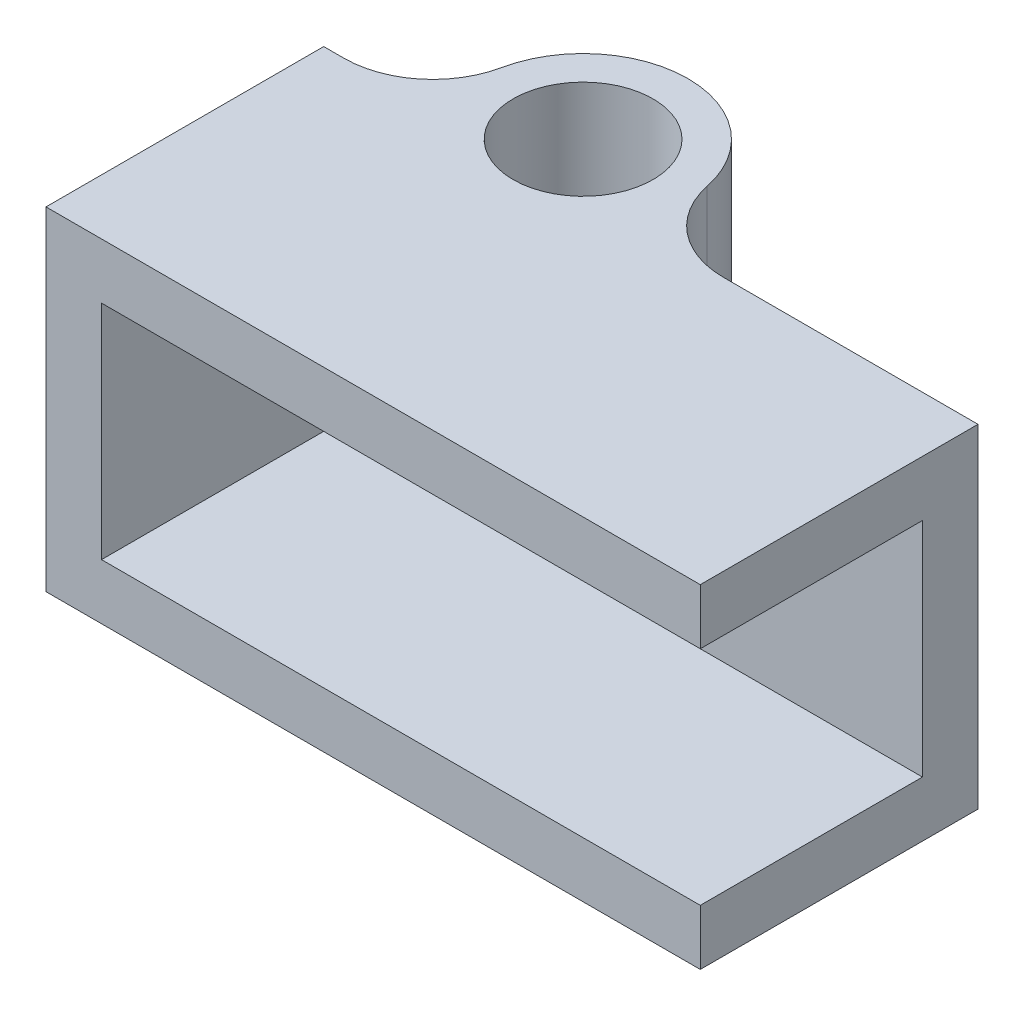
SolidWorks part; units mm, degrees
material "LWPLA"
ref_plane "Front Plane" through (0, 0, 0) normal (0, 0, 1) x (1, 0, 0)
ref_plane "Top Plane" through (0, 0, 0) normal (0, 1, 0) x (1, 0, 0)
ref_plane "Right Plane" through (0, 0, 0) normal (1, 0, 0) x (0, 0, -1)
sketch "Sketch1" plane through (0, 0, 0) normal (0, 1, 0) x (1, 0, 0)
  line L0 (-12.7, -3) -> (12.7, -3)
  line L1 (-12.7, -3) -> (-12.7, -1.4125)
  line L2 (-12.7, -1.4125) -> (-2.6467, -1.4125)
  line L3 (0, -3) -> (0, 3) construction
  line L4 (12.7, -3) -> (12.7, -1.4125)
  line L5 (12.7, -1.4125) -> (2.6467, -1.4125)
  line L6 (0, -3) -> (-6, -3)
  line L7 (-6, -3) -> (-6, -1.4125)
  circle A0 centre (0, 0) radius 2
  circle A1 centre (0, 0) radius 3
  point P7 (0, -3)
  dimension "D1" = 4
  dimension "D2" = 6
  dimension "D3" = 25.4
  dimension "D4" = 1.5875
  dimension "D5" = 6
extrude "Boss-Extrude1" add sketch "Sketch1" along normal blind 9.525 contours A1 L2 L7 L0 | A1 L0 L4 L5 | L3 A1 A0 | A1 L3 A0
fillet "Fillet1" radius 2.54 2 edges at (-2.6467, 4.7625, 1.4125) (2.6467, 4.7625, 1.4125)
sketch "Sketch2" plane through (0, 0, 3) normal (0, 0, 1) x (1, 0, 0)
  line L0 (12.7, 0) -> (-6, 0)
  line L1 (-6, 0) -> (-6, 9.525)
  line L2 (-6, 9.525) -> (12.7, 9.525)
  line L3 (12.7, 9.525) -> (12.7, 7.9375)
  line L4 (12.7, 9.525) -> (12.7, 0) construction
  line L5 (-6, 7.9375) -> (-4.4125, 7.9375) construction
  line L6 (12.7, 7.9375) -> (-4.4125, 7.9375)
  line L7 (-6, 4.7625) -> (12.7, 4.7625) construction
  line L8 (12.7, 0) -> (12.7, 1.5875)
  line L9 (12.7, 1.5875) -> (-4.4125, 1.5875)
  line L10 (-4.4125, 1.5875) -> (-4.4125, 7.9375)
  line L11 (-6, 9.525) -> (-6, 0) construction
  line L12 (12.7, 9.525) -> (12.7, 0) construction
  point P17 (0, 0)
  point P18 (0, 0)
  point P19 (0, 0)
  point P20 (0, 0)
  point P21 (0, 0)
  point P22 (0, 0)
  point P24 (0, 0)
  point P27 (0, 0)
  point P28 (0, 0)
  point P29 (0, 0)
  point P30 (0, 0)
  dimension "D1" = 1.5875
  dimension "D2" = 1.5875
extrude "Boss-Extrude2" add sketch "Sketch2" along normal blind 6.35
